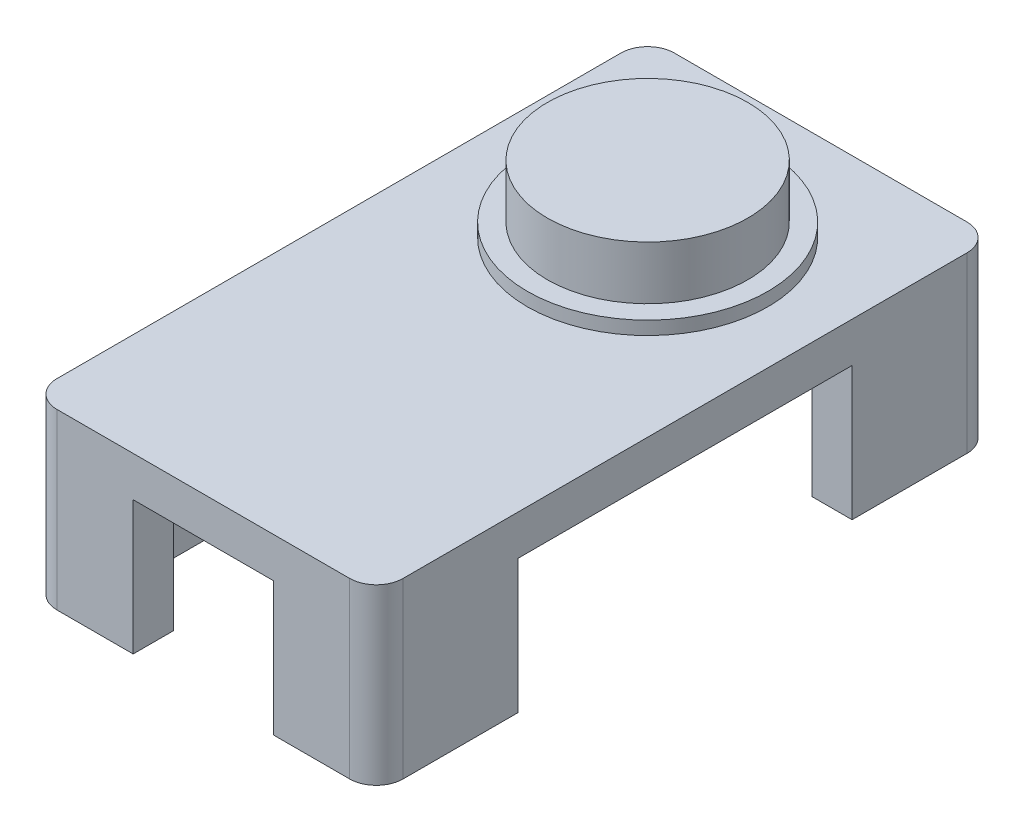
SolidWorks part; units mm, degrees
ref_plane "Alzado" through (0, 0, 0) normal (0, 0, 1) x (1, 0, 0)
ref_plane "Planta" through (0, 0, 0) normal (0, 1, 0) x (1, 0, 0)
ref_plane "Vista lateral" through (0, 0, 0) normal (1, 0, 0) x (0, 0, -1)
sketch "Croquis1" plane through (0, 0, 0) normal (0, 1, 0) x (1, 0, 0)
  line L1 (-9.95, 20.1) -> (9.95, 20.1)
  line L2 (-9.95, 20.1) -> (-9.95, -20.1)
  line L3 (-9.95, -20.1) -> (9.95, -20.1)
  line L4 (9.95, 20.1) -> (9.95, -20.1)
  line L5 (-9.95, 20.1) -> (9.95, -20.1) construction
  line L6 (-9.95, -20.1) -> (9.95, 20.1) construction
  line L7 (-12.95, 23.1) -> (12.95, 23.1)
  line L8 (-12.95, 23.1) -> (-12.95, -23.1)
  line L9 (-12.95, -23.1) -> (12.95, -23.1)
  line L10 (12.95, 23.1) -> (12.95, -23.1)
  line L11 (-12.95, 23.1) -> (12.95, -23.1) construction
  line L12 (-12.95, -23.1) -> (12.95, 23.1) construction
  point P0 (0, 0)
  point P6 (0, 0)
  dimension "D1" = 19.9
  dimension "D2" = 40.2
  dimension "D3" = 3
  dimension "D4" = 3
extrude "Saliente-Extruir1" add sketch "Croquis1" along normal blind 10
sketch "Croquis2" plane through (0, 10, 0) normal (0, 1, 0) x (1, 0, 0)
  line L1 (-12.95, 23.1) -> (12.95, 23.1)
  line L2 (-12.95, 23.1) -> (-12.95, -23.1)
  line L3 (-12.95, -23.1) -> (12.95, -23.1)
  line L4 (12.95, 23.1) -> (12.95, -23.1)
  line L5 (-12.95, 23.1) -> (12.95, -23.1) construction
  line L6 (-12.95, -23.1) -> (12.95, 23.1) construction
  point P0 (0, 0)
extrude "Saliente-Extruir2" add sketch "Croquis2" along normal blind 3
sketch "Croquis3" plane through (0, 10, 0) normal (0, -1, 0) x (1, 0, 0)
  line L0 (12.95, -23.1) -> (-12.95, -23.1) construction
  line L1 (-5.25, 23.1) -> (5.25, 23.1)
  line L2 (-5.25, 23.1) -> (-5.25, -23.1)
  line L3 (-5.25, -23.1) -> (5.25, -23.1)
  line L4 (5.25, 23.1) -> (5.25, -23.1)
  line L5 (-5.25, 23.1) -> (5.25, -23.1) construction
  line L6 (-5.25, -23.1) -> (5.25, 23.1) construction
  point P0 (0, 0)
  dimension "D1" = 10.5
extrude "Cortar-Extruir1" cut sketch "Croquis3" along normal blind 17
sketch "Croquis4" plane through (0, 10, 0) normal (0, -1, 0) x (1, 0, 0)
  line L0 (12.95, 23.1) -> (12.95, -23.1) construction
  line L1 (-12.95, 12.5) -> (12.95, 12.5)
  line L2 (-12.95, 12.5) -> (-12.95, -12.5)
  line L3 (-12.95, -12.5) -> (12.95, -12.5)
  line L4 (12.95, 12.5) -> (12.95, -12.5)
  line L5 (-12.95, 12.5) -> (12.95, -12.5) construction
  line L6 (-12.95, -12.5) -> (12.95, 12.5) construction
  point P0 (0, 0)
  dimension "D1" = 25
extrude "Cortar-Extruir2" cut sketch "Croquis4" along normal blind 17
sketch "Croquis5" plane through (0, 13, 0) normal (0, 1, 0) x (1, 0, 0)
  line L0 (0, 23.1) -> (0, 10.15) construction
  line L1 (12.95, 23.1) -> (-12.95, 23.1) construction
  circle A0 centre (0, 10.15) radius 7.5
  dimension "D2" = 15
  dimension "D1" = 12.95
extrude "Saliente-Extruir3" add sketch "Croquis5" along normal blind 5
sketch "Croquis6" plane through (0, 13, 0) normal (0, 1, 0) x (1, 0, 0)
  circle A0 centre (0, 10.15) radius 9
  dimension "D1" = 18
extrude "Saliente-Extruir4" add sketch "Croquis6" along normal blind 1
fillet "Redondeo1" radius 2 4 edges at (12.95, 6.5, 23.1) (-12.95, 6.5, 23.1) (-12.95, 6.5, -23.1) (12.95, 6.5, -23.1)
